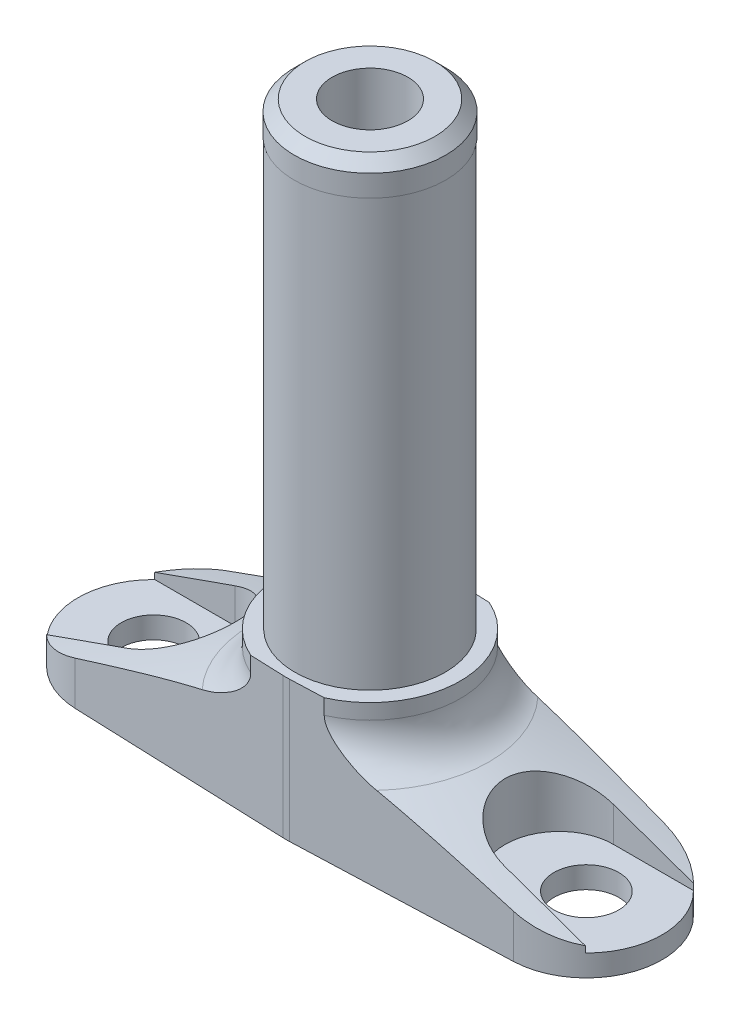
SolidWorks part; units mm, degrees
material "7075-T6 (SN)"
ref_plane "Płaszczyzna XY" through (0, 0, 0) normal (0, 0, 1) x (1, 0, 0)
ref_plane "Płaszczyzna XZ" through (0, 0, 0) normal (0, 1, 0) x (1, 0, 0)
ref_plane "Płaszczyzna YZ" through (0, 0, 0) normal (1, 0, 0) x (0, 0, -1)
sketch "Szkic1" plane through (0, 0, 0) normal (0, 0, 1) x (1, 0, 0)
  line L0 (0, 0) -> (0, 25) construction
  line L1 (0, 0) -> (0, 25)
  line L2 (0, 0) -> (27, 0)
  line L4 (0, 25) -> (27, 25)
  line L5 (27, 0) -> (27, 25)
  dimension "D1" = 54
  dimension "D2" = 25
revolve "Obrót1" add sketch "Szkic1" angle 360 about L0
sketch "Szkic2" plane through (0, 0, 0) normal (0, 0, 1) x (1, 0, 0)
  line L0 (0, 0) -> (0, 25) construction
  line L1 (27, 25) -> (-27, 25) construction
  line L2 (0, 25) -> (8.35, 25) construction
  line L3 (8.35, 25) -> (8.35, 8.788)
  line L4 (8.35, 8.788) -> (27, 2)
  line L5 (27, 0) -> (27, 25) construction
  line L6 (-27, 0) -> (27, 0) construction
  line L7 (8.35, 25) -> (27, 25)
  line L8 (27, 25) -> (27, 2)
  dimension "D1" = 2
  dimension "D2" = 20
  dimension "D3" = 16.7
revolve "Wycięcie-obrót1" cut sketch "Szkic2" angle 360 about L0
fillet "Zaokrąglenie1" radius 4 1 edges at (0, 8.788, -8.35)
ref_plane "Płaszczyzna1" through (0, 2, 0) normal (0, 1, 0) x (1, 0, 0)
sketch "Szkic4" plane through (0, 2, 0) normal (0, 1, 0) x (1, 0, 0)
  line L0 (0, 8.8242) -> (0, -11.1289) construction
  circle A0 centre (-20, 0) radius 3
  circle A1 centre (20, 0) radius 3
  dimension "D1" = 6
  dimension "D2" = 6
  dimension "D3" = 40
extrude "Wytnij-wyciągnięcie3" cut sketch "Szkic4" against normal through all and the other way through all
sketch "Szkic3" plane through (0, 2, 0) normal (0, 1, 0) x (1, 0, 0)
  line L0 (-17.5, 5) -> (-26.533, 5)
  line L13 (-17.5, -5) -> (-26.533, -5)
  line L14 (17.5, 5) -> (26.533, 5)
  line L15 (17.5, -5) -> (26.533, -5)
  line L16 (0, 21.1527) -> (0, -20.0817) construction
  arc A1 (-17.5, -5) -> (-17.5, 5) centre (-17.5, 0) ccw
  arc A2 (17.5, 5) -> (17.5, -5) centre (17.5, 0) ccw
  circle A3 centre (0, 0) radius 27 construction
  arc A4 (-26.533, 5) -> (-26.533, -5) centre (0, 0) ccw
  arc A5 (26.533, -5) -> (26.533, 5) centre (0, 0) ccw
  dimension "D1" = 10
  dimension "D2" = 10
  dimension "D3" = 35
extrude "Wytnij-wyciągnięcie2" cut sketch "Szkic3" along normal through all
sketch "Szkic5" plane through (0, 0, 0) normal (0, -1, 0) x (1, 0, 0)
  line L0 (-20.2625, 6.9951) -> (-0.2906, 7.7445)
  line L1 (-20.2625, -6.9951) -> (-0.2906, -7.7445)
  line L2 (0.2906, 7.7445) -> (20.2625, 6.9951)
  line L3 (20.2625, -6.9951) -> (0.2906, -7.7445)
  arc A0 (-0.2906, -7.7445) -> (0.2906, -7.7445) centre (0, 0) ccw
  arc A1 (-20.2625, 6.9951) -> (-20.2625, -6.9951) centre (-20, 0) ccw
  arc A2 (20.2625, -6.9951) -> (20.2625, 6.9951) centre (20, 0) ccw
  circle A3 centre (0, 0) radius 27 construction
  arc A4 (0.2906, 7.7445) -> (-0.2906, 7.7445) centre (0, 0) ccw
  dimension "D1" = 15.5
extrude "Wytnij-wyciągnięcie4" cut sketch "Szkic5" against normal through all flip side to cut
sketch "Szkic8" plane through (0, 0, 0) normal (0, 0, 1) x (1, 0, 0)
  line L2 (0, 25) -> (0, 13)
  line L5 (0, 13) -> (8.35, 13)
  line L6 (8.35, 11.5889) -> (8.35, 25) construction
  line L7 (8.35, 13) -> (8.35, 25)
  line L8 (8.35, 25) -> (0, 25)
  dimension "D1" = 12
revolve "Wycięcie-obrót2" cut sketch "Szkic8" angle 360 about L2
sketch "Szkic9" plane through (0, 0, 0) normal (0, 0, 1) x (1, 0, 0)
  line L2 (0, 13) -> (0, 55.4234) construction
  line L3 (0, 55.4234) -> (6, 55.4234)
  line L5 (6, 55.4234) -> (7, 54.4234)
  line L6 (0, 55.4234) -> (7, 55.4234)
  line L7 (0, 55.4234) -> (0, 52.4234) construction
  line L8 (6.95, 52.4234) -> (7, 52.4234)
  line L9 (7, 54.4234) -> (7, 52.4234)
  line L10 (0, 13) -> (0, 55.4234)
  line L11 (6.95, 52.4234) -> (6.95, 13)
  line L12 (6.95, 13) -> (0, 13)
  line L13 (3.3965, 13) -> (0.2906, 13) construction
  dimension "D1" = 6.95
  dimension "D2" = 0
  dimension "D3" = 14
  dimension "D4" = 3
  dimension "D5" = 52.4234
revolve "Obrót2" add sketch "Szkic9" angle 360 about L2
sketch "Szkic10" plane through (0, 55.4234, 0) normal (0, 1, 0) x (1, 0, 0)
  circle A0 centre (0, 0) radius 3.5
  dimension "D1" = 7
extrude "Wytnij-wyciągnięcie5" cut sketch "Szkic10" against normal through all
equation "\"D3@Szkic3\"=40-2*1/2*5"
